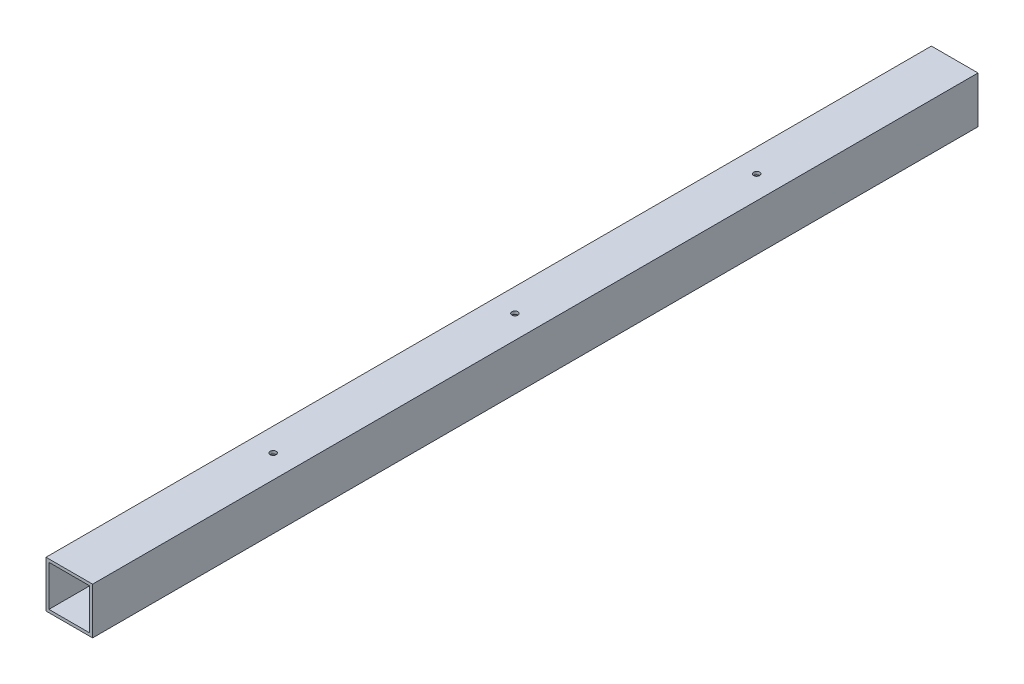
SolidWorks part; units mm, degrees
material "6061 Alloy"
ref_plane "Front Plane" through (0, 0, 0) normal (0, 0, 1) x (1, 0, 0)
ref_plane "Top Plane" through (0, 0, 0) normal (0, 1, 0) x (1, 0, 0)
ref_plane "Right Plane" through (0, 0, 0) normal (1, 0, 0) x (0, 0, -1)
sketch "Sketch1" plane through (0, 0, 0) normal (0, 0, 1) x (1, 0, 0)
  line L0 (-22.225, 3.175) -> (-22.225, 47.625)
  line L1 (-25.4, 0) -> (25.4, 0)
  line L2 (-25.4, 0) -> (-25.4, 50.8)
  line L3 (-25.4, 50.8) -> (25.4, 50.8)
  line L4 (25.4, 0) -> (25.4, 50.8)
  line L5 (-22.225, 47.625) -> (22.225, 47.625)
  line L6 (22.225, 3.175) -> (22.225, 47.625)
  line L7 (-22.225, 3.175) -> (22.225, 3.175)
  dimension "D1" = 50.8
  dimension "D2" = 50.8
  dimension "D3" = 3.175
extrude "Boss-Extrude1" add sketch "Sketch1" along normal blind 965.2
sketch "Sketch2" plane through (0, 50.8, 0) normal (0, 1, 0) x (1, 0, 0)
  line L0 (25.4, 0) -> (-25.4, 0) construction
  line L1 (25.4, -965.2) -> (25.4, 0) construction
  circle A0 centre (0, -215.9) radius 3.302
  circle A1 centre (0, -479.425) radius 3.302
  circle A2 centre (0, -742.95) radius 3.302
  dimension "D1" = 215.9
  dimension "D3" = 6.604
  dimension "D2" = 25.4
  dimension "D5" = 263.525
  dimension "D4" = 3
extrude "Cut-Extrude1" cut sketch "Sketch2" against normal through all
